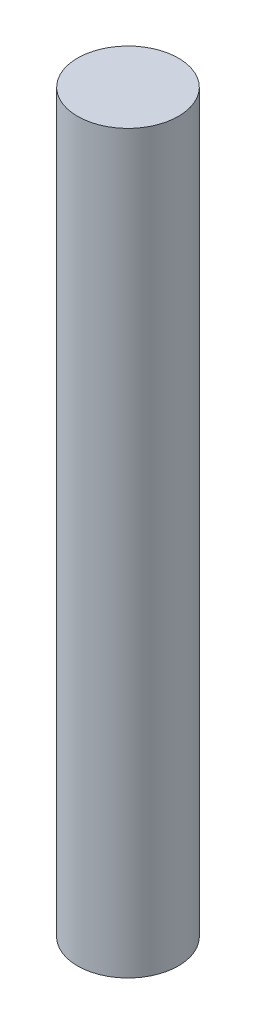
SolidWorks part; units mm, degrees
ref_plane "Ebene vorne" through (0, 0, 0) normal (0, 0, 1) x (1, 0, 0)
ref_plane "Ebene oben" through (0, 0, 0) normal (0, 1, 0) x (1, 0, 0)
ref_plane "Ebene rechts" through (0, 0, 0) normal (1, 0, 0) x (0, 0, -1)
sketch "Skizze1" plane through (0, 0, 0) normal (0, 1, 0) x (1, 0, 0)
  circle A0 centre (0, 0) radius 2.4
  dimension "5" = 4.8
extrude "Aufsatz-Linear austragen1" add sketch "Skizze1" along normal blind 35
